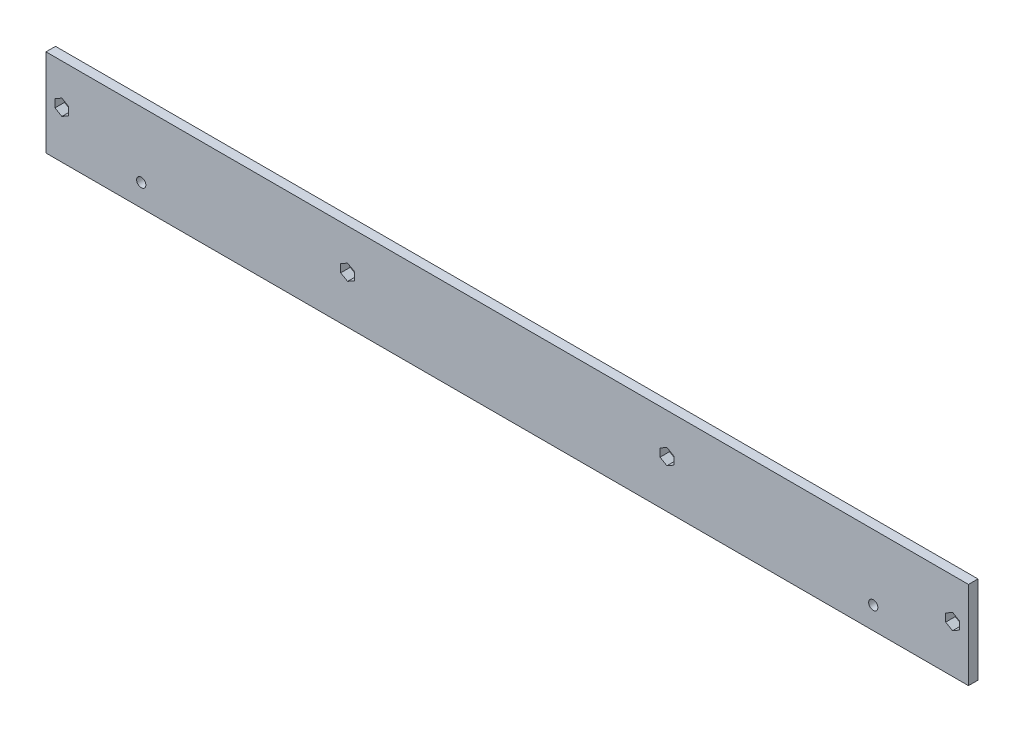
SolidWorks part; units mm, degrees
ref_plane "Plane1" through (0, 0, 0) normal (0, 0, 1) x (1, 0, 0)
ref_plane "Plane2" through (0, 0, 0) normal (0, 1, 0) x (1, 0, 0)
ref_plane "Plane3" through (0, 0, 0) normal (1, 0, 0) x (0, 0, -1)
sketch "Esquisse5" plane through (0, 0, 0) normal (0, 0, 1) x (1, 0, 0)
  line L5 (-3.927, 27.625) -> (286.6703, 27.625)
  line L6 (-3.927, 27.625) -> (-3.927, 0)
  line L7 (-3.927, 0) -> (286.6703, 0)
  line L8 (286.6703, 27.625) -> (286.6703, 0)
  circle A0 centre (281.6703, 15) radius 1.1
  circle A1 centre (91.073, 15) radius 1.1
  circle A2 centre (1.073, 15) radius 1.1
  circle A3 centre (191.6703, 15) radius 1.1
  dimension "D1" = 290.5973
  dimension "D3" = 2.2
  dimension "D2" = 27.625
  dimension "D4" = 5
  dimension "D5" = 90
  dimension "D6" = 5
  dimension "D7" = 90
  dimension "D8" = 15
  dimension "D9" = 3.927
extrude "Extrusion1" add sketch "Esquisse5" along normal blind 3
sketch "Esquisse4" plane through (0, 0, 3) normal (0, 0, 1) x (1, 0, 0)
  line L0 (-3.927, 0) -> (286.6703, 0) construction
  line L1 (-3.927, 27.625) -> (-3.927, 0) construction
  line L2 (286.6703, 0) -> (286.6703, 27.625) construction
  circle A0 centre (26.073, 7) radius 1.45
  circle A2 centre (256.6703, 7) radius 1.45
  dimension "D1" = 2.9
  dimension "D2" = 7
  dimension "D3" = 30
  dimension "D4" = 30
extrude "Enlèv. mat.-Extru.2" cut sketch "Esquisse4" against normal through all
sketch "Esquisse6" plane through (0, 0, 0) normal (0, 0, -1) x (-1, 0, 0)
  line L0 (3.927, 27.625) -> (3.927, 0) construction
  line L1 (-1.073, 12.5) -> (1.0921, 13.75)
  line L2 (1.0921, 13.75) -> (1.0921, 16.25)
  line L3 (1.0921, 16.25) -> (-1.073, 17.5)
  line L4 (-1.073, 17.5) -> (-3.2381, 16.25)
  line L5 (-3.2381, 16.25) -> (-3.2381, 13.75)
  line L6 (-3.2381, 13.75) -> (-1.073, 12.5)
  line L7 (-286.6703, 0) -> (-286.6703, 27.625) construction
  line L14 (-88.9079, 13.75) -> (-88.9079, 16.25)
  line L15 (-88.9079, 16.25) -> (-91.073, 17.5)
  line L16 (-91.073, 17.5) -> (-93.2381, 16.25)
  line L17 (-93.2381, 16.25) -> (-93.2381, 13.75)
  line L18 (-93.2381, 13.75) -> (-91.073, 12.5)
  line L19 (-91.073, 12.5) -> (-88.9079, 13.75)
  line L20 (-189.5053, 13.75) -> (-189.5053, 16.25)
  line L21 (-189.5053, 16.25) -> (-191.6703, 17.5)
  line L22 (-191.6703, 17.5) -> (-193.8354, 16.25)
  line L23 (-193.8354, 16.25) -> (-193.8354, 13.75)
  line L24 (-193.8354, 13.75) -> (-191.6703, 12.5)
  line L25 (-191.6703, 12.5) -> (-189.5053, 13.75)
  line L26 (-279.5053, 13.75) -> (-279.5053, 16.25)
  line L27 (-279.5053, 16.25) -> (-281.6703, 17.5)
  line L28 (-281.6703, 17.5) -> (-283.8354, 16.25)
  line L29 (-283.8354, 16.25) -> (-283.8354, 13.75)
  line L30 (-283.8354, 13.75) -> (-281.6703, 12.5)
  line L31 (-281.6703, 12.5) -> (-279.5053, 13.75)
  circle A0 centre (-1.073, 15) radius 2.1651 construction
  circle A2 centre (-91.073, 15) radius 2.1651 construction
  circle A3 centre (-191.6703, 15) radius 2.1651 construction
  circle A4 centre (-281.6703, 15) radius 2.1651 construction
  dimension "D2" = 2.5
  dimension "D1" = 2.5
  dimension "D3" = 2.5
  dimension "D4" = 2.5
extrude "Enlèv. mat.-Extru.3" cut sketch "Esquisse6" against normal through all
